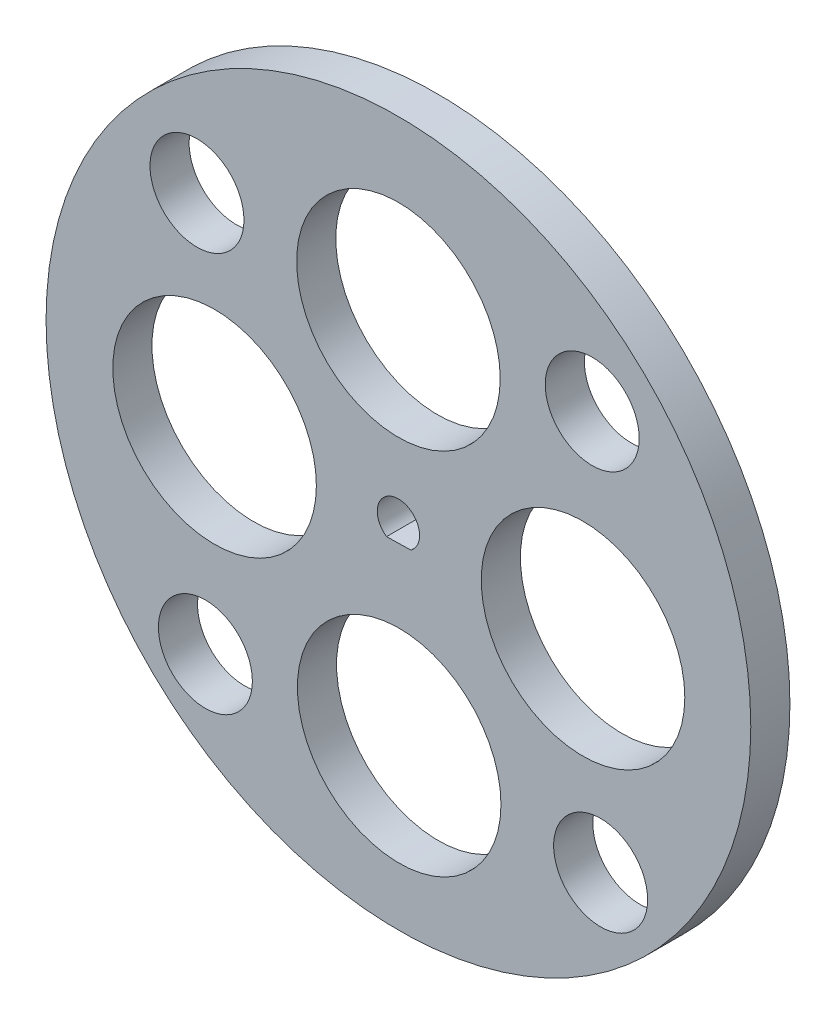
SolidWorks part; units mm, degrees
ref_plane "Plan de face" through (0, 0, 0) normal (0, 0, 1) x (1, 0, 0)
ref_plane "Plan de dessus" through (0, 0, 0) normal (0, 1, 0) x (1, 0, 0)
ref_plane "Plan de droite" through (0, 0, 0) normal (1, 0, 0) x (0, 0, -1)
sketch "Esquisse1" plane through (0, 0, 0) normal (0, 0, 1) x (1, 0, 0)
  line L0 (-1.566, -1.2061) -> (1.5633, -1.1401)
  circle A0 centre (-0.0477, 1.0266) radius 45
  arc A1 (1.5633, -1.1401) -> (-1.566, -1.2061) centre (-0.0477, 1.0266) ccw
  circle A2 centre (-0.0477, 23.5266) radius 13
  circle A3 centre (23.5266, 0.0477) radius 13
  circle A4 centre (0.0477, -23.5266) radius 13
  circle A5 centre (-23.5266, -0.0477) radius 13
  circle A6 centre (24.701, 25.7753) radius 6
  circle A7 centre (25.7753, -24.701) radius 6
  circle A8 centre (-24.701, -25.7753) radius 6
  circle A9 centre (-25.7753, 24.701) radius 6
  point P15 (0, 0)
  point P24 (0, 0)
  dimension "D1" = 22.5
  dimension "D3" = 35
  dimension "D5" = 3.13
  dimension "D6" = 2.7
  dimension "D7" = 90
  dimension "D8" = 26
  dimension "D9" = 12
  dimension "D4" = 4
  dimension "D2" = 4
extrude "Boss.-Extru.1" add sketch "Esquisse1" along normal blind 5
